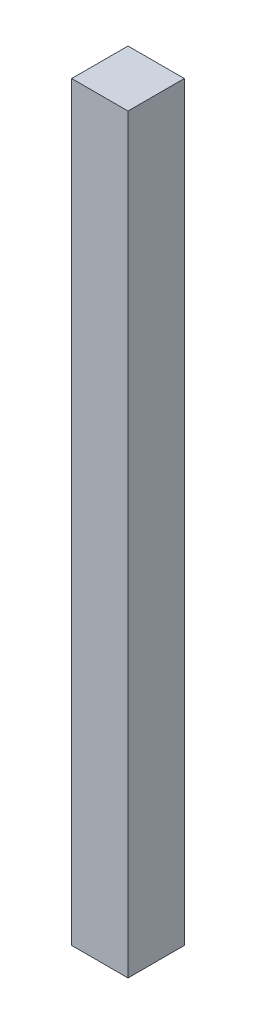
SolidWorks part; units mm, degrees
ref_plane "Front Plane" through (0, 0, 0) normal (0, 0, 1) x (1, 0, 0)
ref_plane "Top Plane" through (0, 0, 0) normal (0, 1, 0) x (1, 0, 0)
ref_plane "Right Plane" through (0, 0, 0) normal (1, 0, 0) x (0, 0, -1)
sketch "Sketch1" plane through (0, 0, 0) normal (0, 1, 0) x (1, 0, 0)
  line L1 (7.5, 7.5) -> (-7.5, 7.5)
  line L2 (7.5, 7.5) -> (7.5, -7.5)
  line L3 (7.5, -7.5) -> (-7.5, -7.5)
  line L4 (-7.5, 7.5) -> (-7.5, -7.5)
  line L5 (7.5, 7.5) -> (-7.5, -7.5) construction
  line L6 (7.5, -7.5) -> (-7.5, 7.5) construction
  point P0 (0, 0)
  dimension "D1" = 15
  dimension "D2" = 15
extrude "Boss-Extrude1" add sketch "Sketch1" along normal blind 200
